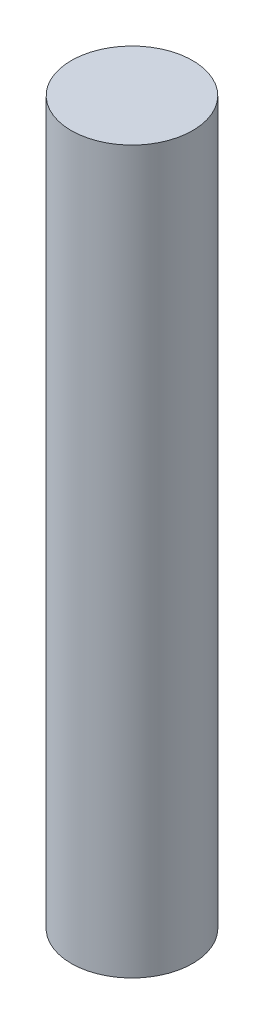
SolidWorks part; units mm, degrees
ref_plane "Front Plane" through (0, 0, 0) normal (0, 0, 1) x (1, 0, 0)
ref_plane "Top Plane" through (0, 0, 0) normal (0, 1, 0) x (1, 0, 0)
ref_plane "Right Plane" through (0, 0, 0) normal (1, 0, 0) x (0, 0, -1)
sketch "Sketch1" plane through (0, 0, 0) normal (0, 1, 0) x (1, 0, 0)
  circle A0 centre (0, 0) radius 3.45
  dimension "D1" = 6.9
extrude "Boss-Extrude1" add sketch "Sketch1" along normal blind 41
